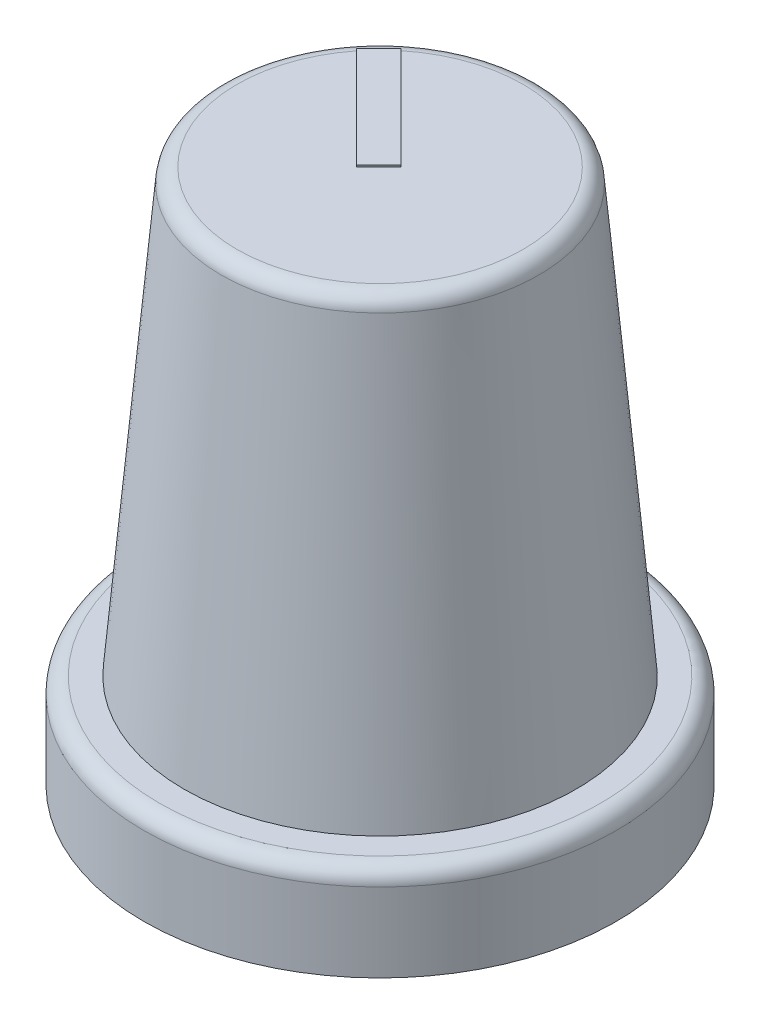
SolidWorks part; units mm, degrees
ref_plane "Front Plane" through (0, 0, 0) normal (0, 0, 1) x (1, 0, 0)
ref_plane "Top Plane" through (0, 0, 0) normal (0, 1, 0) x (1, 0, 0)
ref_plane "Right Plane" through (0, 0, 0) normal (1, 0, 0) x (0, 0, -1)
sketch "Sketch1" plane through (0, 0, 0) normal (0, 1, 0) x (1, 0, 0)
  circle A0 centre (0, 0) radius 7.5
  dimension "D1" = 15
extrude "Boss-Extrude1" add sketch "Sketch1" along normal blind 3
ref_plane "Plane1" through (0, 17, 0) normal (0, 1, 0) x (1, 0, 0)
sketch "Sketch2" plane through (0, 17, 0) normal (0, 1, 0) x (1, 0, 0)
  circle A0 centre (0, 0) radius 5
  dimension "D1" = 10
extrude "Boss-Extrude2" add sketch "Sketch2" against normal up to surface (14 mm away) draft 5
sketch "Sketch4" plane through (0, 0, 0) normal (0, -1, 0) x (1, 0, 0)
  circle A3 centre (0, 0) radius 6.5
  circle A4 centre (0, 0) radius 6.5
  dimension "D1" = 1
extrude "Cut-Extrude1" cut sketch "Sketch4" against normal offset from surface (2 mm away) 1 up to face at (0, 3, 6.2248)
sketch "Sketch5" plane through (0, 2, 0) normal (0, -1, 0) x (1, 0, 0)
  circle A2 centre (0, 0) radius 5.5
  circle A3 centre (0, 0) radius 5.5
  dimension "D1" = 1
extrude "Cut-Extrude2" cut sketch "Sketch5" against normal offset from surface 1 draft 5 up to face at (0, 17, 5)
fillet "Fillet1" radius 0.5 1 edges at (0, 3, 7.5)
fillet "Fillet2" radius 0.5 1 edges at (0, 17, 5)
sketch "Sketch7" plane through (0, 17, 0) normal (0, 1, 0) x (1, 0, 0)
  line L0 (-0.3724, -0.3724) -> (0.3347, 0.3347)
  line L1 (0.3347, 0.3347) -> (-2.8768, 3.5462)
  line L2 (-2.8768, 3.5462) -> (-3.5839, 2.8391)
  line L3 (-3.5839, 2.8391) -> (-0.3724, -0.3724)
  circle A2 centre (0, 0) radius 4.5418 construction
  point P2 (-3.2304, 3.1926)
  dimension "D1" = 1
extrude "Boss-Extrude3" add sketch "Sketch7" along normal blind 0.05
